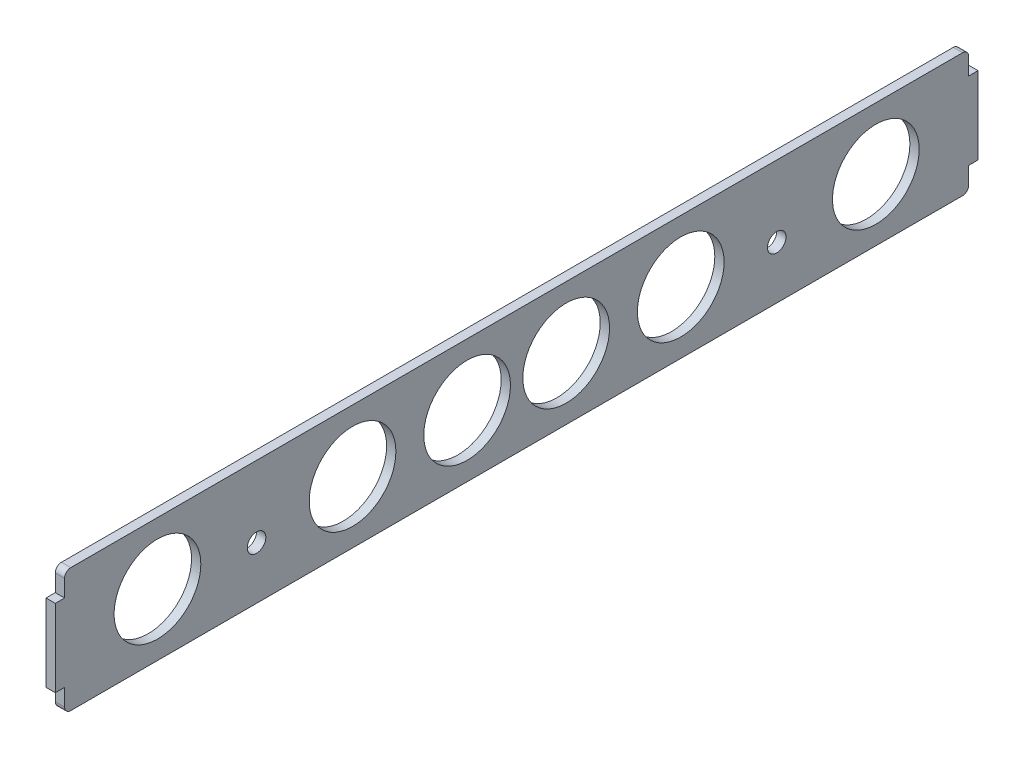
SolidWorks part; units mm, degrees
ref_plane "Front Plane" through (0, 0, 0) normal (0, 0, 1) x (1, 0, 0)
ref_plane "Top Plane" through (0, 0, 0) normal (0, 1, 0) x (1, 0, 0)
ref_plane "Right Plane" through (0, 0, 0) normal (1, 0, 0) x (0, 0, -1)
sketch "Sketch3" plane through (0, 0, 0) normal (1, 0, 0) x (0, 0, -1)
  line L1 (0, 0) -> (292, 0)
  line L2 (0, 0) -> (0, -40)
  line L3 (0, -40) -> (292, -40)
  line L4 (292, 0) -> (292, -40)
  line L5 (22.5, 0) -> (47.5, 0) construction
  line L6 (22.5, 0) -> (22.5, 3) construction
  line L7 (22.5, 3) -> (47.5, 3) construction
  line L8 (47.5, 0) -> (47.5, 3) construction
  line L9 (244.5, 0) -> (269.5, 0) construction
  line L10 (244.5, 0) -> (244.5, 3) construction
  line L11 (244.5, 3) -> (269.5, 3) construction
  line L12 (269.5, 0) -> (269.5, 3) construction
  line L13 (0, -9) -> (3, -9) construction
  line L14 (0, -9) -> (0, -31) construction
  line L15 (0, -31) -> (3, -31) construction
  line L16 (3, -9) -> (3, -31) construction
  line L17 (292, -9) -> (289, -9) construction
  line L18 (292, -9) -> (292, -31) construction
  line L19 (292, -31) -> (289, -31) construction
  line L20 (289, -9) -> (289, -31) construction
  line L21 (66.04, -9) -> (69.04, -9) construction
  line L22 (66.04, -9) -> (66.04, -31) construction
  line L23 (66.04, -31) -> (69.04, -31) construction
  line L24 (69.04, -9) -> (69.04, -31) construction
  line L25 (222.96, -9) -> (225.96, -9) construction
  line L26 (222.96, -9) -> (222.96, -31) construction
  line L27 (222.96, -31) -> (225.96, -31) construction
  line L28 (225.96, -9) -> (225.96, -31) construction
  circle A0 centre (62, -23) radius 3
  circle A1 centre (230, -23) radius 3
  point P29 (67.54, -9)
  point P30 (224.46, -9)
  point P32 (3, -20)
  point P33 (69.04, -20)
  point P34 (225.96, -20)
  point P35 (289, -20)
  point P36 (292, -20)
  point P37 (66.04, -20)
  point P38 (35, 3)
  point P39 (257, 3)
  point P41 (62, -24.099)
  point P42 (0, -20)
  dimension "D14" = 6
  dimension "D16" = 6
  dimension "D1" = 40
  dimension "D2" = 292
  dimension "D3" = 67.54
  dimension "D4" = 67.54
  dimension "D5" = 25
  dimension "D6" = 25
  dimension "D7" = 3
  dimension "D8" = 22
  dimension "D9" = 22
  dimension "D10" = 22
  dimension "D11" = 22
  dimension "D12" = 35
  dimension "D13" = 35
  dimension "D15" = 62
  dimension "D17" = 62
  dimension "D18" = 3
extrude "Boss-Extrude2" add sketch "Sketch3" along normal blind 3 contours L20 L17 L4 L1 L2 L13 L16 L15 L3 L19 L21 L24 L23 L22 L25 L28 L27 L26 | L1 L8 L7 L6 | L1 L12 L11 L10
fillet "Fillet1" radius 2 4 edges at (1.5, 0, -292) (1.5, -40, -292) (1.5, -40, 0) (1.5, 0, 0)
sketch "Sketch4" plane through (3, 0, 0) normal (1, 0, 0) x (0, 0, -1)
  line L0 (0, -20) -> (307.4873, -20) construction
  line L1 (0, -2) -> (0, -38) construction
  line L2 (292, -2) -> (292, -38) construction
  circle A0 centre (30, -20) radius 14
  circle A1 centre (93, -20) radius 14
  circle A2 centre (130, -20) radius 14
  circle A3 centre (162, -20) radius 14
  circle A4 centre (199, -20) radius 14
  circle A5 centre (262, -20) radius 14
  dimension "D1" = 28
  dimension "D3" = 30
  dimension "D2" = 30
  dimension "D4" = 93
  dimension "D5" = 93
  dimension "D6" = 130
  dimension "D7" = 130
extrude "Cut-Extrude1" cut sketch "Sketch4" against normal blind 10
sketch "Sketch5" plane through (3, 0, 0) normal (1, 0, 0) x (0, 0, -1)
  line L0 (0, -2) -> (0, -38) construction
  line L1 (0, -7.5) -> (-3, -7.5)
  line L2 (0, -7.5) -> (0, -32.5)
  line L3 (0, -32.5) -> (-3, -32.5)
  line L4 (-3, -7.5) -> (-3, -32.5)
  line L5 (292, -2) -> (292, -38) construction
  line L6 (292, -7.5) -> (295, -7.5)
  line L7 (292, -7.5) -> (292, -32.5)
  line L8 (292, -32.5) -> (295, -32.5)
  line L9 (295, -7.5) -> (295, -32.5)
  point P12 (295, -20)
  point P13 (-3, -20)
  point P14 (0, -20)
  dimension "D1" = 25
  dimension "D2" = 3
extrude "Boss-Extrude3" add sketch "Sketch5" against normal blind 3
equation "\"D4@Sketch3\"=\"D3@Sketch3\""
equation "\"D6@Sketch3\"=\"D5@Sketch3\""
